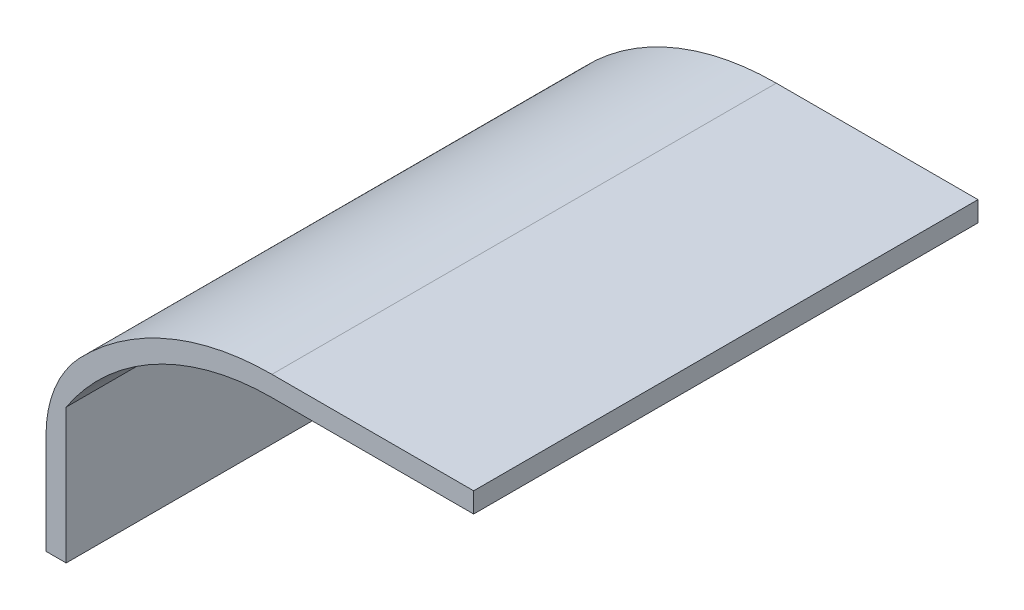
SolidWorks part; units mm, degrees
material "ABS"
ref_plane "Front" through (0, 0, 0) normal (0, 0, 1) x (1, 0, 0)
ref_plane "Top" through (0, 0, 0) normal (0, 1, 0) x (1, 0, 0)
ref_plane "Right" through (0, 0, 0) normal (1, 0, 0) x (0, 0, -1)
sketch "ｽｹｯﾁ1" plane through (0, 0, 0) normal (0, 0, 1) x (1, 0, 0)
  line L0 (-50, 0) -> (50, 0) construction
  line L1 (-50, 61) -> (50, 61) construction
  line L2 (-50, -61) -> (50, -61) construction
  line L3 (0, 61) -> (0, -61) construction
  line L4 (-101, 33.4664) -> (-101, -33.4664) construction
  line L5 (-101, 0) -> (-101, 33.4664)
  line L6 (-50, 61) -> (0, 61)
  line L7 (-106, 0) -> (-106, 34.9285)
  line L8 (-50, 66) -> (0, 66)
  line L9 (-101, 0) -> (-106, 0)
  line L10 (0, 61) -> (0, 66)
  arc A0 (-50, 61) -> (-50, -61) centre (-50, 0) ccw construction
  arc A1 (50, -61) -> (50, 61) centre (50, 0) ccw construction
  arc A2 (-101, 33.4664) -> (-50, 61) centre (-50, 0) cw
  arc A3 (-106, 34.9285) -> (-50, 66) centre (-50, 0) cw
  point P2 (0, 0)
  dimension "D2" = 61
  dimension "D1" = 100
  dimension "D3" = 51
  dimension "D4" = 5
extrude "ﾎﾞｽ - 押し出し1" add sketch "ｽｹｯﾁ1" along normal blind 125
fillet "ﾌｨﾚｯﾄ1" radius 30 1 edges at (-106, 34.9285, 62.5)
